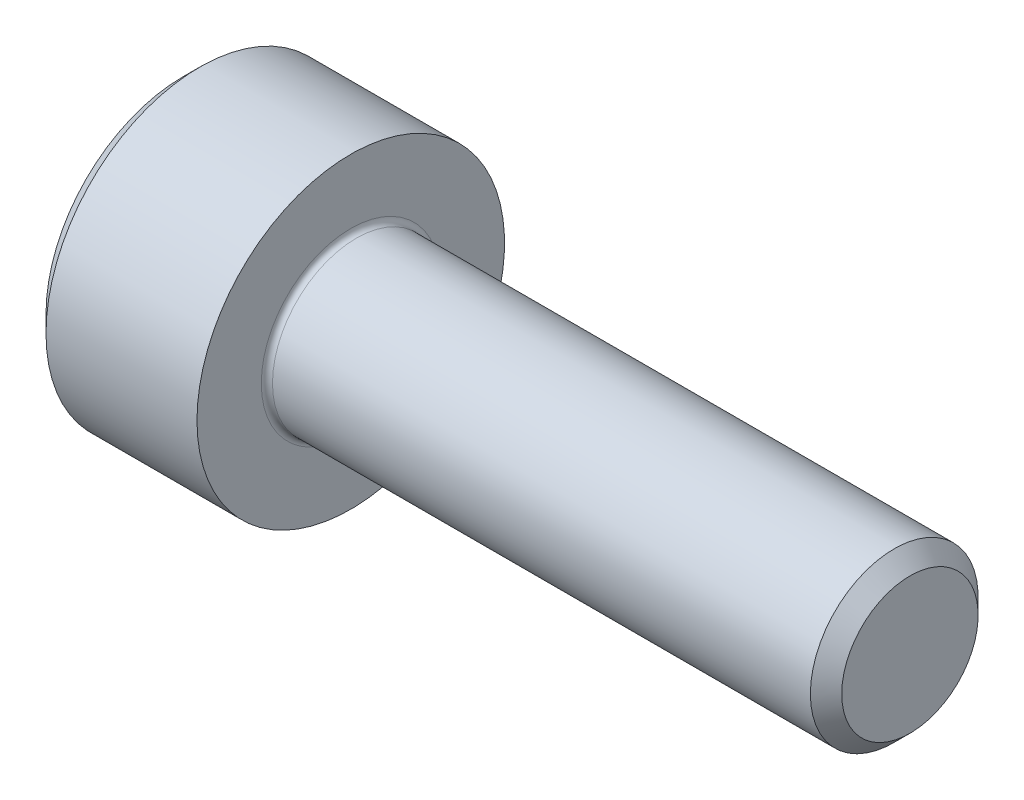
SolidWorks part; units mm, degrees
ref_plane "Plane1" through (0, 0, 0) normal (0, 0, 1) x (1, 0, 0)
ref_plane "Plane2" through (0, 0, 0) normal (0, 1, 0) x (1, 0, 0)
ref_plane "Plane3" through (0, 0, 0) normal (1, 0, 0) x (0, 0, -1)
sketch "BodySke" plane through (0, 0, 0) normal (0, 0, 1) x (1, 0, 0)
  line L0 (0, 0) -> (0, 2.45)
  line L1 (0.3, 2.75) -> (3, 2.75)
  line L2 (3, 2.75) -> (3, 1.5)
  line L3 (3, 1.5) -> (12.7195, 1.5)
  line L4 (13, 1.2195) -> (13, 0)
  line L5 (13, 0) -> (0, 0)
  line L6 (-31.75, 0) -> (127, 0) construction
  line L7 (0, 2.45) -> (0.3, 2.75)
  line L8 (13, 1.2195) -> (12.7195, 1.5)
  line L9 (0, -2.45) -> (0.3, -2.75) construction
  line L10 (13, -1.2195) -> (12.7195, -1.5) construction
  line L11 (3.5, 9.525) -> (3.5, 3.175) construction
  line L12 (3, 9.525) -> (3, 3.175) construction
  line L13 (-37, 9.525) -> (-37, 3.175) construction
  dimension "Diameter" = 3
  dimension "Head_ht" = 3
  dimension "Length" = 10
  dimension "Body_ch_ang" = 45
  dimension "Head_dia" = 5.5
  dimension "Head_ch_ang" = 45
  dimension "Minor_dia" = 2.439
  dimension "Advance" = 0.5
  dimension "Thread_nom" = 10
  dimension "Thread_length" = 50
  dimension "Head_ch_ht" = 0.3
revolve "Base-Revolve" add sketch "BodySke"
cosmetic thread "ThreadCosmetic" [suppressed]
fillet "Fillet1" radius 0.1 1 edges at (3, 0, 1.5)
sketch "Sketch2" plane through (0, 0, 0) normal (0, 0, 1) x (1, 0, 0)
  line L0 (0, 1.28) -> (1.3, 1.28)
  line L1 (1.3, 1.28) -> (2.039, 0)
  line L2 (-31.75, 0) -> (127, 0) construction
  line L3 (2.039, 0) -> (0, 0)
  line L4 (0, 0) -> (0, 1.28)
  line L5 (0, 2.45) -> (0, -2.45) construction
  line L6 (0, 0) -> (47.625, 0) construction
  line L7 (3, -2.75) -> (3, 2.75) construction
  dimension "D1" = 1.28
  dimension "D2" = 60
  dimension "Wall_thickness" = 1.7
revolve "Hex-PreBroach" cut sketch "Sketch2" angle 360 about L6
sketch "Sketch3" plane through (0, 0, 0) normal (-1, 0, 0) x (0, 0.5, 0.866)
  line L0 (0.739, 1.28) -> (-0.739, 1.28)
  line L1 (-0.739, 1.28) -> (-1.478, 0)
  line L2 (0.739, 1.28) -> (1.478, 0)
  line L3 (0.739, -1.28) -> (1.478, 0)
  line L4 (0.739, -1.28) -> (-0.739, -1.28)
  line L5 (-0.739, -1.28) -> (-1.478, 0)
  dimension "D1" = 1.28
  dimension "D2" = 1.28
  dimension "Hex_size" = 2.56
extrude "Hex" cut sketch "Sketch3" against normal blind 1.3
sketch "Sketch4" plane through (0, 0, 0) normal (-1, 0, 0) x (0, 0, 1)
  line L0 (0, 0) -> (1.4605, 0)
  line L1 (0, 0) -> (6.1484, 3.5498) construction
  line L2 (0, 0) -> (0.7302, 1.2648)
  line L3 (1.2009, 0.3267) -> (1.3933, 0.4378)
  line L4 (0.8834, 0.8767) -> (1.0758, 0.9877)
  arc A0 (1.2009, 0.3267) -> (0.8834, 0.8767) centre (0, 0) ccw
  arc A1 (1.4605, 0) -> (1.3933, 0.4378) centre (0, 0) ccw
  arc A2 (0.7302, 1.2648) -> (1.0758, 0.9877) centre (0, 0) cw
  dimension "D1" = 30
  dimension "Spline_n_dim" = 2.4892
  dimension "Spline_m_dim" = 2.921
  dimension "D2" = 60
  dimension "D3" = 0.3175
  dimension "Spline_p_dim" = 0.635
extrude "Spline" [suppressed] cut sketch "Sketch4" against normal blind 1.3
pattern_circular "CirPattern1" [suppressed] count 6 every 60
sketch "Sketch5" plane through (0, 0, 0) normal (0, 0, 1) x (1, 0, 0)
  line L0 (-31.75, 0) -> (127, 0) construction
  line L2 (0, 2.45) -> (0, -2.45) construction
  circle A0 centre (1.2, 0) radius 0.475
  dimension "Drilled_hole_dia" = 0.95
  dimension "Drilled_hole_loc" = 1.2
extrude "Hole" [suppressed] cut sketch "Sketch5" against normal through all and the other way through all
pattern_circular "Drilled-4" [suppressed] count 2 every 60
pattern_circular "Drilled-6" [suppressed] count 3 every 60
sketch "ThdSchSke" plane through (0, 0, 0) normal (0, 0, 1) x (1, 0, 0)
  line L0 (3.5, -1.2195) -> (3.3036, -1.5)
  line L1 (3.5, -1.2195) -> (3.6964, -1.5)
  line L2 (3.6964, -1.5) -> (3.6964, -1.875)
  line L3 (-3.175, 0) -> (5.1513, 0) construction
  line L5 (3.6964, -1.875) -> (3.3036, -1.875)
  line L6 (3.3036, -1.875) -> (3.3036, -1.5)
  line L7 (0, 2.45) -> (0, -2.45) construction
  dimension "Thread_minor" = 2.439
  dimension "Diameter" = 3
  dimension "Start" = 3.5
  dimension "SideAngle" = 55
  dimension "VeeAngle" = 70
  dimension "Overcut" = 3.75
revolve "ThreadSchematic" [suppressed] cut sketch "ThdSchSke" angle 360 about L3
pattern_linear "ThdSchPat" [suppressed]
equation "\"D2@Sketch3\" = \"Hex_size@Sketch3\" / 2"
equation "\"D1@Sketch3\" = \"Hex_size@Sketch3\" / 2"
equation "\"D1@Sketch2\" = \"Hex_size@Sketch3\" / 2"
equation "\"D3@Sketch4\" = \"Spline_p_dim@Sketch4\" / 2"
equation "\"Thread_minor@ThreadCosmetic\"  =  \"Minor_dia@BodySke\""
equation "\"D2@CirPattern1\" = 360 / \"Num_teeth@CirPattern1\""
equation "\"Wall_thickness@Sketch2\" = \"Head_ht@BodySke\" - \"Key_eng@Hex\""
equation "\"Thread_length@ThreadCosmetic\" = ((sgn( (\"Length@BodySke\" - \"Advance@BodySke\" ) - \"Thread_nom@BodySke\" )-1)*( (\"Length@BodySke\" - \"Advance@BodySke\" ) - \"Thread_nom@BodySke\" ))/-2+ \"Thread_nom@BodySke\""
equation "\"Thread_minor@ThdSchSke\" = \"Minor_dia@BodySke\""
equation "\"Diameter@ThdSchSke\" = \"Diameter@BodySke\""
equation "\"Overcut@ThdSchSke\" = \"Diameter@BodySke\" * 1.25"
equation "\"Start@ThdSchSke\" = \"Head_ht@BodySke\" + \"Length@BodySke\" - \"Thread_length@ThreadCosmetic\"  '---Non-countersunk---"
equation "\"Num_threads@ThdSchPat\" = int( \"Thread_length@ThreadCosmetic\" / \"Advance@BodySke\" + 0.999 )  + 1"
equation "\"Advance@ThdSchPat\" = \"Thread_length@ThreadCosmetic\" /  (\"Num_threads@ThdSchPat\" - 1) 'relax it"
equation "\"Num_threads@ThdSchPat\" = \"Num_threads@ThdSchPat\" - sgn( \"Num_threads@ThdSchPat\" - 1) '---chamfered tips only---"
